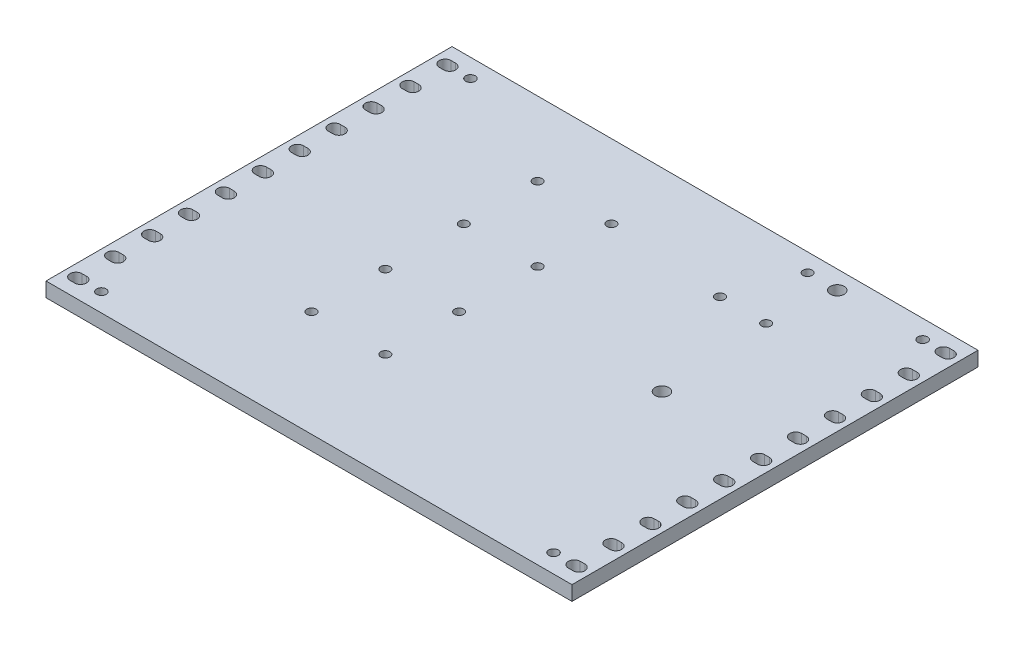
SolidWorks part; units mm, degrees
other "Markup1"
sketch "Sketch3" plane through (330.2, 10, 0) normal (0.0623, 0.8147, 0.5765) x (0.9973, -0.0285, -0.0676)
material "Polyurethane Foam Rigid"
ref_plane "Front Plane" through (0, 0, 0) normal (0, 0, 1) x (1, 0, 0)
ref_plane "Top Plane" through (0, 0, 0) normal (0, 1, 0) x (1, 0, 0)
ref_plane "Right Plane" through (0, 0, 0) normal (1, 0, 0) x (0, 0, -1)
sketch "Sketch1" plane through (0, 0, 0) normal (0, 1, 0) x (1, 0, 0)
  line L1 (0, 0) -> (361.95, 0)
  line L2 (0, 0) -> (0, 279.4)
  line L3 (0, 279.4) -> (361.95, 279.4)
  line L4 (361.95, 0) -> (361.95, 279.4)
  line L5 (38.1, 0) -> (292.1, 0)
  dimension "D1" = 361.95
  dimension "D2" = 279.4
extrude "Boss-Extrude1" add sketch "Sketch1" along normal blind 10
sketch "Sketch2" plane through (0, 10, 0) normal (0, 1, 0) x (1, 0, 0)
  line L0 (352.425, 279.4) -> (352.425, 0)
  line L1 (0, 279.4) -> (361.95, 279.4) construction
  line L2 (0, 0) -> (361.95, 0) construction
  line L3 (350.8375, 266.7) -> (354.0125, 266.7) construction
  line L5 (350.8375, 270.764) -> (354.0125, 270.764)
  line L6 (350.8375, 262.636) -> (354.0125, 262.636)
  line L7 (352.425, 266.7) -> (352.425, 241.3) construction
  line L8 (180.975, 279.4) -> (180.975, 0) construction
  line L13 (350.8375, 241.3) -> (354.0125, 241.3) construction
  line L14 (350.8375, 245.364) -> (354.0125, 245.364)
  line L15 (350.8375, 237.236) -> (354.0125, 237.236)
  line L16 (350.8375, 215.9) -> (354.0125, 215.9) construction
  line L17 (350.8375, 219.964) -> (354.0125, 219.964)
  line L18 (350.8375, 211.836) -> (354.0125, 211.836)
  line L19 (350.8375, 190.5) -> (354.0125, 190.5) construction
  line L20 (350.8375, 194.564) -> (354.0125, 194.564)
  line L21 (350.8375, 186.436) -> (354.0125, 186.436)
  line L22 (350.8375, 165.1) -> (354.0125, 165.1) construction
  line L23 (350.8375, 169.164) -> (354.0125, 169.164)
  line L24 (350.8375, 161.036) -> (354.0125, 161.036)
  line L25 (350.8375, 139.7) -> (354.0125, 139.7) construction
  line L26 (350.8375, 143.764) -> (354.0125, 143.764)
  line L27 (350.8375, 135.636) -> (354.0125, 135.636)
  line L28 (350.8375, 114.3) -> (354.0125, 114.3) construction
  line L29 (350.8375, 118.364) -> (354.0125, 118.364)
  line L30 (350.8375, 110.236) -> (354.0125, 110.236)
  line L31 (350.8375, 88.9) -> (354.0125, 88.9) construction
  line L32 (350.8375, 92.964) -> (354.0125, 92.964)
  line L33 (350.8375, 84.836) -> (354.0125, 84.836)
  line L34 (350.8375, 63.5) -> (354.0125, 63.5) construction
  line L35 (350.8375, 67.564) -> (354.0125, 67.564)
  line L36 (350.8375, 59.436) -> (354.0125, 59.436)
  line L37 (350.8375, 38.1) -> (354.0125, 38.1) construction
  line L38 (350.8375, 42.164) -> (354.0125, 42.164)
  line L39 (350.8375, 34.036) -> (354.0125, 34.036)
  line L40 (350.8375, 12.7) -> (354.0125, 12.7) construction
  line L41 (350.8375, 16.764) -> (354.0125, 16.764)
  line L42 (350.8375, 8.636) -> (354.0125, 8.636)
  line L43 (11.1125, 266.7) -> (7.9375, 266.7) construction
  line L44 (11.1125, 270.764) -> (7.9375, 270.764)
  line L45 (11.1125, 262.636) -> (7.9375, 262.636)
  line L46 (11.1125, 12.7) -> (7.9375, 12.7) construction
  line L47 (11.1125, 16.764) -> (7.9375, 16.764)
  line L48 (11.1125, 8.636) -> (7.9375, 8.636)
  line L49 (11.1125, 38.1) -> (7.9375, 38.1) construction
  line L50 (11.1125, 42.164) -> (7.9375, 42.164)
  line L51 (11.1125, 34.036) -> (7.9375, 34.036)
  line L52 (11.1125, 63.5) -> (7.9375, 63.5) construction
  line L53 (11.1125, 67.564) -> (7.9375, 67.564)
  line L54 (11.1125, 59.436) -> (7.9375, 59.436)
  line L55 (11.1125, 88.9) -> (7.9375, 88.9) construction
  line L56 (11.1125, 92.964) -> (7.9375, 92.964)
  line L57 (11.1125, 84.836) -> (7.9375, 84.836)
  line L58 (11.1125, 114.3) -> (7.9375, 114.3) construction
  line L59 (11.1125, 118.364) -> (7.9375, 118.364)
  line L60 (11.1125, 110.236) -> (7.9375, 110.236)
  line L61 (11.1125, 139.7) -> (7.9375, 139.7) construction
  line L62 (11.1125, 143.764) -> (7.9375, 143.764)
  line L63 (11.1125, 135.636) -> (7.9375, 135.636)
  line L64 (11.1125, 165.1) -> (7.9375, 165.1) construction
  line L65 (11.1125, 169.164) -> (7.9375, 169.164)
  line L66 (11.1125, 161.036) -> (7.9375, 161.036)
  line L67 (11.1125, 190.5) -> (7.9375, 190.5) construction
  line L68 (11.1125, 194.564) -> (7.9375, 194.564)
  line L69 (11.1125, 186.436) -> (7.9375, 186.436)
  line L70 (11.1125, 215.9) -> (7.9375, 215.9) construction
  line L71 (11.1125, 219.964) -> (7.9375, 219.964)
  line L72 (11.1125, 211.836) -> (7.9375, 211.836)
  line L73 (11.1125, 241.3) -> (7.9375, 241.3) construction
  line L74 (11.1125, 245.364) -> (7.9375, 245.364)
  line L75 (11.1125, 237.236) -> (7.9375, 237.236)
  line L76 (361.95, 0) -> (361.95, 279.4) construction
  arc A30 (350.8375, 270.764) -> (350.8375, 262.636) centre (350.8375, 266.7) ccw
  arc A31 (354.0125, 262.636) -> (354.0125, 270.764) centre (354.0125, 266.7) ccw
  arc A45 (350.8375, 245.364) -> (350.8375, 237.236) centre (350.8375, 241.3) ccw
  arc A46 (354.0125, 237.236) -> (354.0125, 245.364) centre (354.0125, 241.3) ccw
  arc A47 (350.8375, 219.964) -> (350.8375, 211.836) centre (350.8375, 215.9) ccw
  arc A48 (354.0125, 211.836) -> (354.0125, 219.964) centre (354.0125, 215.9) ccw
  arc A49 (350.8375, 194.564) -> (350.8375, 186.436) centre (350.8375, 190.5) ccw
  arc A50 (354.0125, 186.436) -> (354.0125, 194.564) centre (354.0125, 190.5) ccw
  arc A51 (350.8375, 169.164) -> (350.8375, 161.036) centre (350.8375, 165.1) ccw
  arc A52 (354.0125, 161.036) -> (354.0125, 169.164) centre (354.0125, 165.1) ccw
  arc A53 (350.8375, 143.764) -> (350.8375, 135.636) centre (350.8375, 139.7) ccw
  arc A54 (354.0125, 135.636) -> (354.0125, 143.764) centre (354.0125, 139.7) ccw
  arc A55 (350.8375, 118.364) -> (350.8375, 110.236) centre (350.8375, 114.3) ccw
  arc A56 (354.0125, 110.236) -> (354.0125, 118.364) centre (354.0125, 114.3) ccw
  arc A57 (350.8375, 92.964) -> (350.8375, 84.836) centre (350.8375, 88.9) ccw
  arc A58 (354.0125, 84.836) -> (354.0125, 92.964) centre (354.0125, 88.9) ccw
  arc A59 (350.8375, 67.564) -> (350.8375, 59.436) centre (350.8375, 63.5) ccw
  arc A60 (354.0125, 59.436) -> (354.0125, 67.564) centre (354.0125, 63.5) ccw
  arc A61 (350.8375, 42.164) -> (350.8375, 34.036) centre (350.8375, 38.1) ccw
  arc A62 (354.0125, 34.036) -> (354.0125, 42.164) centre (354.0125, 38.1) ccw
  arc A63 (350.8375, 16.764) -> (350.8375, 8.636) centre (350.8375, 12.7) ccw
  arc A64 (354.0125, 8.636) -> (354.0125, 16.764) centre (354.0125, 12.7) ccw
  arc A65 (11.1125, 270.764) -> (11.1125, 262.636) centre (11.1125, 266.7) cw
  arc A66 (7.9375, 262.636) -> (7.9375, 270.764) centre (7.9375, 266.7) cw
  arc A67 (11.1125, 16.764) -> (11.1125, 8.636) centre (11.1125, 12.7) cw
  arc A68 (7.9375, 8.636) -> (7.9375, 16.764) centre (7.9375, 12.7) cw
  arc A69 (11.1125, 42.164) -> (11.1125, 34.036) centre (11.1125, 38.1) cw
  arc A70 (7.9375, 34.036) -> (7.9375, 42.164) centre (7.9375, 38.1) cw
  arc A71 (11.1125, 67.564) -> (11.1125, 59.436) centre (11.1125, 63.5) cw
  arc A72 (7.9375, 59.436) -> (7.9375, 67.564) centre (7.9375, 63.5) cw
  arc A73 (11.1125, 92.964) -> (11.1125, 84.836) centre (11.1125, 88.9) cw
  arc A74 (7.9375, 84.836) -> (7.9375, 92.964) centre (7.9375, 88.9) cw
  arc A75 (11.1125, 118.364) -> (11.1125, 110.236) centre (11.1125, 114.3) cw
  arc A76 (7.9375, 110.236) -> (7.9375, 118.364) centre (7.9375, 114.3) cw
  arc A77 (11.1125, 143.764) -> (11.1125, 135.636) centre (11.1125, 139.7) cw
  arc A78 (7.9375, 135.636) -> (7.9375, 143.764) centre (7.9375, 139.7) cw
  arc A79 (11.1125, 169.164) -> (11.1125, 161.036) centre (11.1125, 165.1) cw
  arc A80 (7.9375, 161.036) -> (7.9375, 169.164) centre (7.9375, 165.1) cw
  arc A81 (11.1125, 194.564) -> (11.1125, 186.436) centre (11.1125, 190.5) cw
  arc A82 (7.9375, 186.436) -> (7.9375, 194.564) centre (7.9375, 190.5) cw
  arc A83 (11.1125, 219.964) -> (11.1125, 211.836) centre (11.1125, 215.9) cw
  arc A84 (7.9375, 211.836) -> (7.9375, 219.964) centre (7.9375, 215.9) cw
  arc A85 (11.1125, 245.364) -> (11.1125, 237.236) centre (11.1125, 241.3) cw
  arc A86 (7.9375, 237.236) -> (7.9375, 245.364) centre (7.9375, 241.3) cw
  point P8 (352.425, 266.7)
  point P19 (352.425, 241.3)
  point P26 (352.425, 215.9)
  point P33 (352.425, 190.5)
  point P40 (352.425, 165.1)
  point P49 (352.425, 139.7)
  point P56 (352.425, 114.3)
  point P63 (352.425, 88.9)
  point P70 (352.425, 63.5)
  point P77 (352.425, 38.1)
  point P84 (352.425, 12.7)
  point P90 (9.525, 266.7)
  point P97 (9.525, 12.7)
  point P104 (9.525, 38.1)
  point P111 (9.525, 63.5)
  point P118 (9.525, 88.9)
  point P125 (9.525, 114.3)
  point P132 (9.525, 139.7)
  point P139 (9.525, 165.1)
  point P146 (9.525, 190.5)
  point P153 (9.525, 215.9)
  point P160 (9.525, 241.3)
  point P167 (0, 0)
  dimension "D3" = 3.175
  dimension "D1" = 9.525
  dimension "D2" = 8.128
  dimension "D4" = 12.7
  dimension "D5" = 11
extrude "Cut-Extrude1" cut sketch "Sketch2" against normal through all and the other way through all contours L41 A63 L42 L0 | L42 A64 L41 L0 | L39 A62 L38 L0
sketch "Sketch4" plane through (0, 0, 0) normal (0, -1, 0) x (1, 0, 0)
  line L1 (0, -279.4) -> (361.95, -279.4) construction
  line L2 (361.95, 0) -> (361.95, -279.4) construction
  circle A0 centre (277.8125, -266.7) radius 4.7625
  circle A1 centre (277.8125, -146.05) radius 4.7625
  dimension "D1" = 84.1375
  dimension "D3" = 9.525
  dimension "D2" = 12.7
  dimension "D4" = 120.65
extrude "Cut-Extrude2" cut sketch "Sketch4" against normal through all
sketch "Sketch5" plane through (0, 0, 0) normal (0, -1, 0) x (1, 0, 0)
  line L0 (361.95, 0) -> (361.95, -279.4) construction
  line L1 (0, -279.4) -> (361.95, -279.4) construction
  circle A3 centre (257.175, -266.9441) radius 3.175
  circle A4 centre (273.05, -222.4941) radius 3.175
  circle A5 centre (241.3, -222.4941) radius 3.175
  point P1 (0, 0)
  point P3 (0, 0)
  point P5 (0, 0)
  point P12 (350.1022, -278.3505)
  dimension "D6" = 6.35
  dimension "D1" = 15.875
  dimension "D2" = 88.9
  dimension "D3" = 31.75
  dimension "D4" = 56.9059
  dimension "D5" = 12.4559
extrude "Cut-Extrude3" cut sketch "Sketch5" against normal through all
sketch "Sketch6" plane through (0, 0, 0) normal (0, -1, 0) x (1, 0, 0)
  line L1 (109.697, -228.6) -> (109.697, -73.025) construction
  line L2 (361.95, 0) -> (361.95, -279.4) construction
  line L3 (0, -279.4) -> (361.95, -279.4) construction
  line L4 (160.497, -228.6) -> (160.497, -73.025) construction
  circle A4 centre (109.697, -228.6) radius 3.175
  circle A5 centre (109.697, -177.8) radius 3.175
  circle A6 centre (109.697, -123.825) radius 3.175
  circle A7 centre (109.697, -73.025) radius 3.175
  circle A8 centre (160.497, -228.6) radius 3.175
  circle A9 centre (160.497, -177.8) radius 3.175
  circle A10 centre (160.497, -123.825) radius 3.175
  circle A11 centre (160.497, -73.025) radius 3.175
  point P1 (0, 0)
  point P3 (0, 0)
  point P12 (0, 0)
  point P14 (124.9032, -229.0126)
  point P16 (123.209, -274.1277)
  point P25 (160.497, -150.8125)
  point P26 (109.697, -150.8125)
  dimension "D1" = 252.253
  dimension "D6" = 6.35
  dimension "D2" = 50.8
  dimension "D3" = 101.6
  dimension "D4" = 50.8
  dimension "D5" = 50.8
  dimension "D7" = 50.8
extrude "Cut-Extrude4" cut sketch "Sketch6" against normal through all
sketch "Sketch7" plane through (0, 0, 0) normal (0, -1, 0) x (1, 0, 0)
  line L0 (361.95, 0) -> (361.95, -279.4) construction
  line L1 (0, 0) -> (361.95, 0) construction
  line L2 (0, 0) -> (0, -279.4) construction
  circle A4 centre (25.4, -266.7) radius 3.302
  circle A5 centre (336.55, -266.7) radius 3.302
  circle A6 centre (336.55, -12.7) radius 3.302
  circle A7 centre (25.4, -12.7) radius 3.302
  point P5 (0, 0)
  point P12 (0, 0)
  point P14 (0, 0)
  point P15 (0, 0)
  point P16 (0, 0)
  dimension "D1" = 25.4
  dimension "D3" = 25.4
  dimension "D2" = 12.7
extrude "Cut-Extrude5" cut sketch "Sketch7" against normal through all
